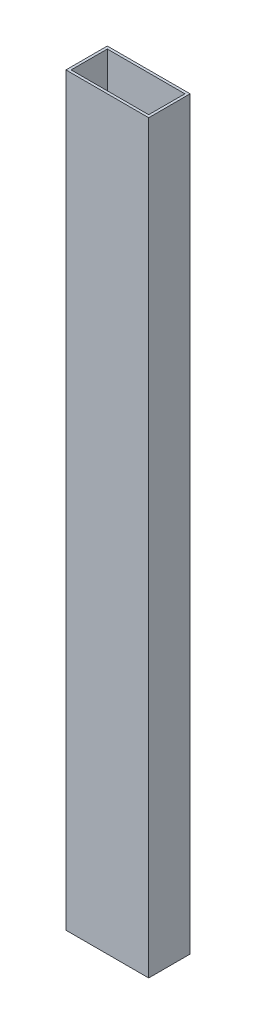
SolidWorks part; units mm, degrees
ref_plane "Front Plane" through (0, 0, 0) normal (0, 0, 1) x (1, 0, 0)
ref_plane "Top Plane" through (0, 0, 0) normal (0, 1, 0) x (1, 0, 0)
ref_plane "Right Plane" through (0, 0, 0) normal (1, 0, 0) x (0, 0, -1)
ref_plane "Plane1" through (0, 228.6, 0) normal (0, 1, 0) x (1, 0, 0)
sketch "Sketch1" plane through (0, 228.6, 0) normal (0, 1, 0) x (1, 0, 0)
  line L0 (-5.905, -18.3451) -> (-5.905, 3.8799)
  line L1 (-5.905, 3.8799) -> (41.72, 3.8799)
  line L2 (41.72, 3.8799) -> (41.72, -18.3451)
  line L3 (41.72, -18.3451) -> (-5.905, -18.3451)
  line L4 (43.3075, 5.4674) -> (-7.4925, 5.4674)
  line L5 (-7.4925, 5.4674) -> (-7.4925, -19.9326)
  line L6 (-7.4925, -19.9326) -> (43.3075, -19.9326)
  line L7 (43.3075, -19.9326) -> (43.3075, 5.4674)
  dimension "D1" = 1.5875
  dimension "D2" = 1.5875
  dimension "D3" = 50.8
  dimension "D4" = 25.4
  dimension "D5" = 1.5875
  dimension "D6" = 1.5875
extrude "Boss-Extrude1" add sketch "Sketch1" against normal blind 457.2
